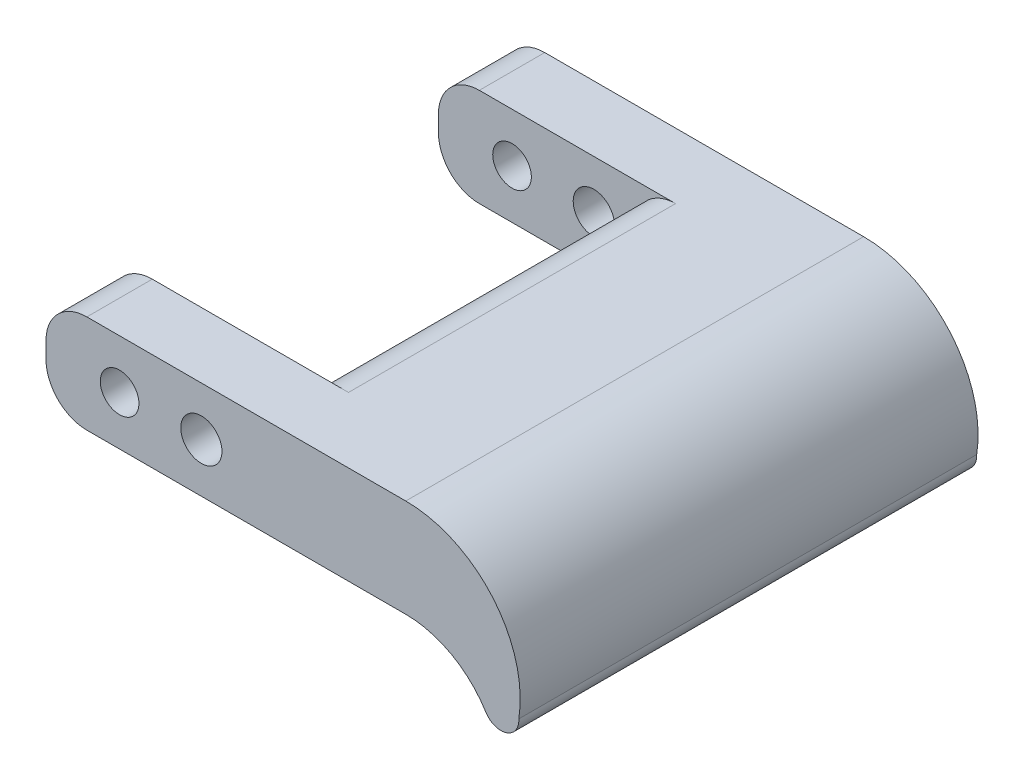
SolidWorks part; units mm, degrees
ref_plane "Front Plane" through (0, 0, 0) normal (0, 0, 1) x (1, 0, 0)
ref_plane "Top Plane" through (0, 0, 0) normal (0, 1, 0) x (1, 0, 0)
ref_plane "Right Plane" through (0, 0, 0) normal (1, 0, 0) x (0, 0, -1)
sketch "Sketch1" plane through (0, 0, 0) normal (0, 1, 0) x (1, 0, 0)
  line L1 (0, 0) -> (27.94, 0)
  line L2 (0, 0) -> (0, 35.56)
  line L3 (0, 35.56) -> (27.94, 35.56)
  line L4 (27.94, 0) -> (27.94, 35.56)
  line L5 (0, 30.48) -> (15.24, 30.48)
  line L6 (0, 30.48) -> (0, 5.08)
  line L7 (0, 5.08) -> (15.24, 5.08)
  line L8 (15.24, 30.48) -> (15.24, 5.08)
  dimension "D1" = 35.56
  dimension "D2" = 27.94
  dimension "D3" = 25.4
  dimension "D4" = 5.08
  dimension "D5" = 15.24
extrude "Boss-Extrude1" add sketch "Sketch1" along normal blind 7.62 contours L5 L8 L7 L2 L1 L4 L3
fillet "Fillet1" radius 3.175 6 edges at (15.24, 7.62, -17.78) (15.24, 0, -17.78) (0, 0, -33.02) (0, 7.62, -33.02) (0, 0, -2.54) (0, 7.62, -2.54)
sketch "Sketch2" plane through (0, 0, 0) normal (0, 0, 1) x (1, 0, 0)
  line L0 (3.175, 7.62) -> (27.94, 7.62) construction
  line L1 (0, 4.445) -> (0, 3.175) construction
  circle A0 centre (5.715, 3.81) radius 1.5
  circle A1 centre (12.065, 3.81) radius 1.6
  dimension "D1" = 3
  dimension "D2" = 3.2
  dimension "D3" = 6.35
  dimension "D4" = 3.81
  dimension "D5" = 5.715
extrude "Cut-Extrude1" cut sketch "Sketch2" against normal through all
sketch "Sketch3" plane through (0, 0, 0) normal (0, 0, 1) x (1, 0, 0)
  line L0 (3.175, 0) -> (27.94, 0) construction
  line L1 (3.175, 7.62) -> (27.94, 7.62) construction
  line L2 (27.94, 0) -> (27.94, 7.62)
  arc A0 (27.94, 7.62) -> (36.7224, -2.6472) centre (27.94, -1.2697) cw
  arc A1 (27.94, 0) -> (34.1531, -3.4652) centre (27.94, -7.3027) cw
  arc A2 (34.1531, -3.4652) -> (36.7224, -2.6472) centre (35.3355, -2.7349) ccw
extrude "Boss-Extrude2" add sketch "Sketch3" against normal up to vertex (35.56 mm away) contours A1 A2 A0 L2 up to point (27.94, 0, -35.56)
